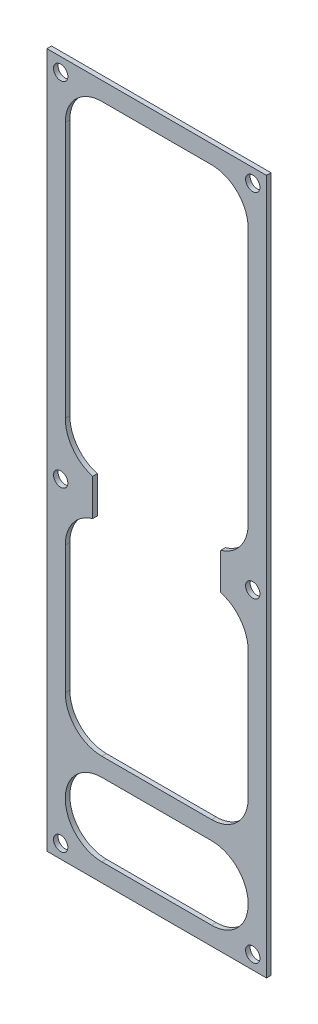
SolidWorks part; units mm, degrees
ref_plane "Front Plane" through (0, 0, 0) normal (0, 0, 1) x (1, 0, 0)
ref_plane "Top Plane" through (0, 0, 0) normal (0, 1, 0) x (1, 0, 0)
ref_plane "Right Plane" through (0, 0, 0) normal (1, 0, 0) x (0, 0, -1)
sketch "Sketch1" plane through (0, 0, 0) normal (0, 0, 1) x (1, 0, 0)
  line L1 (0, 0) -> (76.2, 0)
  line L2 (0, 0) -> (0, -241.3)
  line L3 (0, -241.3) -> (76.2, -241.3)
  line L4 (76.2, 0) -> (76.2, -241.3)
  dimension "D1" = 76.2
  dimension "D2" = 241.3
extrude "Boss-Extrude1" add sketch "Sketch1" along normal blind 1.5875
sketch "Sketch2" plane through (0, 0, 1.5875) normal (0, 0, 1) x (1, 0, 0)
  line L0 (19.05, -6.35) -> (57.15, -6.35)
  line L1 (69.85, -19.05) -> (69.85, -107.95)
  line L2 (6.35, -19.05) -> (6.35, -107.95)
  line L3 (76.2, 0) -> (0, 0) construction
  line L4 (0, 0) -> (0, -241.3) construction
  line L5 (19.05, -234.95) -> (57.15, -234.95)
  line L6 (19.05, -209.55) -> (57.15, -209.55)
  line L7 (0, -241.3) -> (76.2, -241.3) construction
  line L8 (76.2, -241.3) -> (76.2, 0) construction
  line L9 (19.05, -203.2) -> (57.15, -203.2)
  line L10 (69.85, -190.5) -> (69.85, -146.05)
  line L11 (6.35, -190.5) -> (6.35, -146.05)
  line L12 (15.875, -120.65) -> (15.875, -133.35)
  line L13 (60.325, -120.65) -> (60.325, -133.35)
  arc A0 (57.15, -234.95) -> (57.15, -209.55) centre (57.15, -222.25) ccw
  arc A1 (19.05, -234.95) -> (19.05, -209.55) centre (19.05, -222.25) cw
  arc A2 (19.05, -6.35) -> (6.35, -19.05) centre (19.05, -19.05) ccw
  arc A3 (57.15, -6.35) -> (69.85, -19.05) centre (57.15, -19.05) cw
  arc A4 (57.15, -203.2) -> (69.85, -190.5) centre (57.15, -190.5) ccw
  arc A5 (19.05, -203.2) -> (6.35, -190.5) centre (19.05, -190.5) cw
  arc A6 (6.35, -146.05) -> (15.875, -133.35) centre (19.5792, -146.05) cw
  arc A7 (6.35, -107.95) -> (15.875, -120.65) centre (19.5792, -107.95) ccw
  arc A8 (69.85, -107.95) -> (60.325, -120.65) centre (56.6208, -107.95) cw
  arc A9 (69.85, -146.05) -> (60.325, -133.35) centre (56.6208, -146.05) ccw
  point P16 (6.35, -222.25)
  point P17 (69.85, -222.25)
  point P26 (6.35, -6.35)
  point P29 (69.85, -6.35)
  dimension "D4" = 6.35
  dimension "D8" = 12.7
  dimension "D10" = 12.7
  dimension "D18" = 13.2292
  dimension "D19" = 44.45
  dimension "D22" = 13.2292
  dimension "D1" = 63.5
  dimension "D2" = 6.35
  dimension "D3" = 6.35
  dimension "D5" = 6.35
  dimension "D6" = 6.35
  dimension "D7" = 25.4
  dimension "D9" = 6.35
  dimension "D11" = 9.525
  dimension "D12" = 12.7
  dimension "D13" = 38.1
  dimension "D14" = 9.525
  dimension "D15" = 44.45
  dimension "D16" = 6.35
  dimension "D17" = 6.35
  dimension "D20" = 38.1
  dimension "D21" = 12.7
extrude "Cut-Extrude1" cut sketch "Sketch2" against normal blind 1.5875
sketch "Sketch3" plane through (0, 0, 1.5875) normal (0, 0, 1) x (1, 0, 0)
  line L0 (4.7625, -4.7625) -> (4.7625, -236.5375) construction
  line L1 (4.7625, -236.5375) -> (71.4375, -236.5375) construction
  line L2 (71.4375, -236.5375) -> (71.4375, -4.7625) construction
  line L3 (71.4375, -4.7625) -> (4.7625, -4.7625) construction
  line L4 (0, 0) -> (0, -241.3) construction
  line L5 (76.2, -241.3) -> (76.2, 0) construction
  line L6 (76.2, 0) -> (0, 0) construction
  line L7 (0, -241.3) -> (76.2, -241.3) construction
  line L9 (19.05, -234.95) -> (57.15, -234.95) construction
  circle A0 centre (4.7625, -4.7625) radius 2.4892
  circle A1 centre (71.4375, -4.7625) radius 2.4892
  circle A2 centre (71.4375, -127) radius 2.4892
  circle A3 centre (4.7625, -127) radius 2.4892
  circle A4 centre (4.7625, -236.5375) radius 2.4892
  circle A5 centre (71.4375, -236.5375) radius 2.4892
  point P12 (71.4375, -127)
  point P14 (4.7625, -127)
  dimension "D6" = 4.9784
  dimension "D1" = 4.7625
  dimension "D2" = 4.7625
  dimension "D3" = 4.7625
  dimension "D4" = 4.7625
  dimension "D5" = 107.95
extrude "Cut-Extrude2" cut sketch "Sketch3" against normal blind 1.5875
